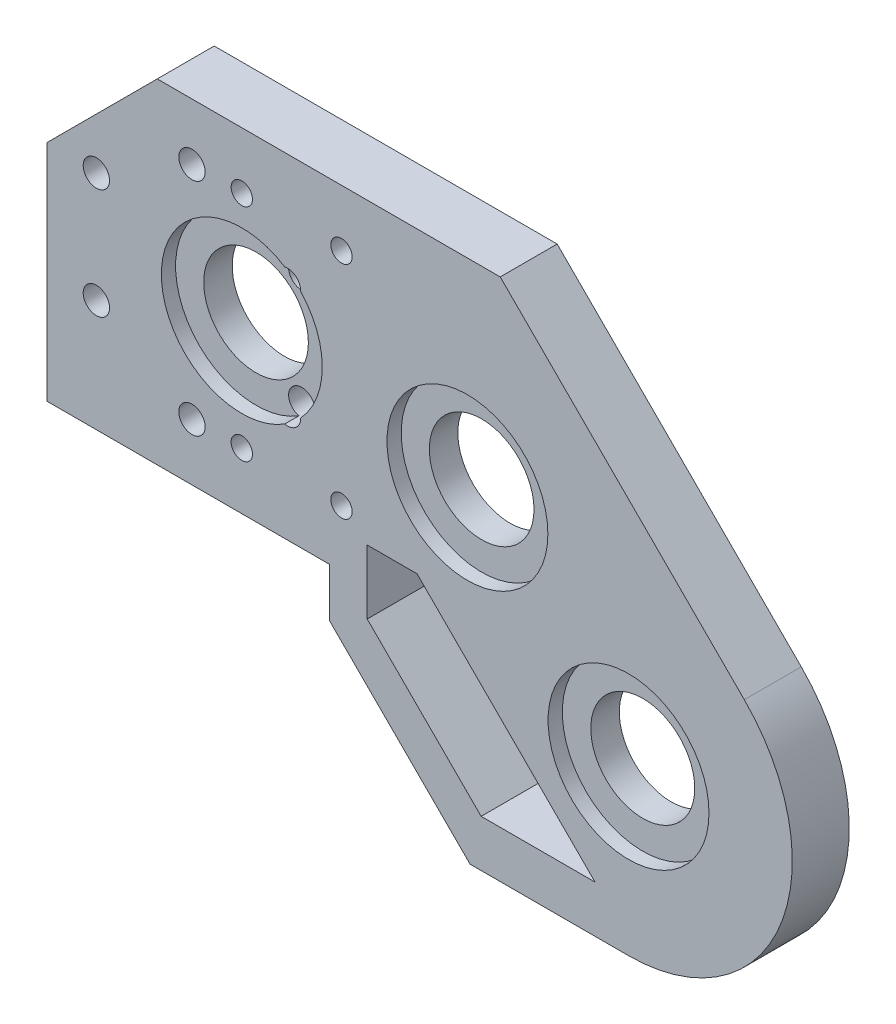
SolidWorks part; units mm, degrees
ref_plane "Plano frontal" through (0, 0, 0) normal (0, 0, 1) x (1, 0, 0)
ref_plane "Plano superior" through (0, 0, 0) normal (0, 1, 0) x (1, 0, 0)
ref_plane "Plano direito" through (0, 0, 0) normal (1, 0, 0) x (0, 0, -1)
sketch "Model" plane through (0, 0, 0) normal (0, 0, 1) x (1, 0, 0)
  line L0 (0, 0) -> (39, 0)
  line L1 (39, 0) -> (39.7, 0)
  line L2 (39.7, 0) -> (39.7, -6.8548)
  line L3 (0, 0) -> (0, 31.4419)
  line L4 (50.1111, 46.949) -> (15.5071, 46.949)
  line L5 (0, 31.4419) -> (15.5071, 46.949)
  line L6 (39.7, -6.8548) -> (52.4452, -19.6)
  line L7 (72, -15) -> (52, 5)
  line L8 (97.9635, 12.6635) -> (63.6779, 46.949)
  line L9 (50.1111, 46.949) -> (63.6779, 46.949)
  line L10 (52.4452, -19.6) -> (59.4452, -26.6)
  line L11 (81.7, -26.6) -> (59.4452, -26.6)
  line L12 (72, -15) -> (77, -20)
  line L13 (52, 5) -> (45, 5)
  line L14 (45, 5) -> (45, -4)
  line L15 (45, -4) -> (61, -20)
  line L16 (61, -20) -> (77, -20)
  circle A2 centre (59.0726, 19.0274) radius 7.35
  arc A5 (81.7, -26.6) -> (97.9635, 12.6635) centre (81.7, -3.6) ccw
  circle A6 centre (81.7, -3.6) radius 7.3
  circle A7 centre (6.9606, 15.731) radius 1.85
  circle A8 centre (6.9606, 31.231) radius 1.85
  circle A9 centre (20.384, 38.981) radius 1.85
  circle A10 centre (33.8074, 31.231) radius 1.85
  circle A11 centre (33.8074, 15.731) radius 1.85
  circle A12 centre (20.384, 7.981) radius 1.85
  circle A13 centre (27.384, 23.481) radius 7.35
sketch "Esboço2" plane through (0, 0, 0) normal (0, 0, 1) x (1, 0, 0)
  circle A15 centre (6.9606, 15.731) radius 3.3
  circle A16 centre (6.9606, 31.231) radius 3.3
  circle A17 centre (33.8074, 15.731) radius 3.3
  circle A18 centre (20.384, 38.981) radius 3.3
  circle A19 centre (33.8074, 31.231) radius 3.3
  circle A20 centre (20.384, 7.981) radius 3.3
sketch "Esboço3" plane through (0, 0, 0) normal (0, 0, 1) x (1, 0, 0)
  circle A3 centre (81.7, -3.6) radius 11.3
  circle A4 centre (59.0726, 19.0274) radius 11.3
  circle A14 centre (27.384, 23.481) radius 11.3
extrude "Ressalto-extrusão1" add sketch "Model" along normal blind 8
sketch "Esboço4" plane through (0, 0, 8) normal (0, 0, 1) x (1, 0, 0)
  circle A3 centre (81.7, -3.6) radius 11.3
  circle A4 centre (59.0726, 19.0274) radius 11.3
  circle A14 centre (27.384, 23.481) radius 11.3
extrude "Corte-extrusão1" cut sketch "Esboço3" along normal blind 2
extrude "Corte-extrusão2" cut sketch "Esboço4" against normal blind 2
extrude "Corte-extrusão4" cut sketch "Esboço2" along normal blind 2
sketch "Esboço6" plane through (0, 0, 0) normal (0, -1, 0) x (1, 0, 0)
  line L0 (39.7, 4) -> (11.8, 4) construction
  line L1 (39.7, 8) -> (39.7, 0) construction
  line L2 (11.8, 4) -> (30.8, 4) construction
  line L3 (30.8, 4) -> (30.8, 8) construction
  line L4 (0, 8) -> (39.7, 8) construction
  circle A0 centre (11.8, 4) radius 1.5
  circle A1 centre (30.8, 4) radius 1.5
extrude "Corte-extrusão5" cut sketch "Esboço6" against normal blind 10
sketch "Esboço7" plane through (0, 0, 8) normal (0, 0, 1) x (1, 0, 0)
  line L0 (20.384, 38.981) -> (27.384, 38.981) construction
  line L1 (27.384, 38.981) -> (27.384, 7.981) construction
  line L2 (27.384, 7.981) -> (41.384, 7.981) construction
  line L3 (41.384, 7.981) -> (41.384, 38.981) construction
  line L4 (41.384, 38.981) -> (27.384, 38.981) construction
  circle A0 centre (27.384, 38.981) radius 1.5
  circle A1 centre (41.384, 38.981) radius 1.5
  circle A2 centre (41.384, 7.981) radius 1.5
  circle A3 centre (27.384, 7.981) radius 1.5
extrude "supoerte_placa" cut sketch "Esboço7" against normal through all
